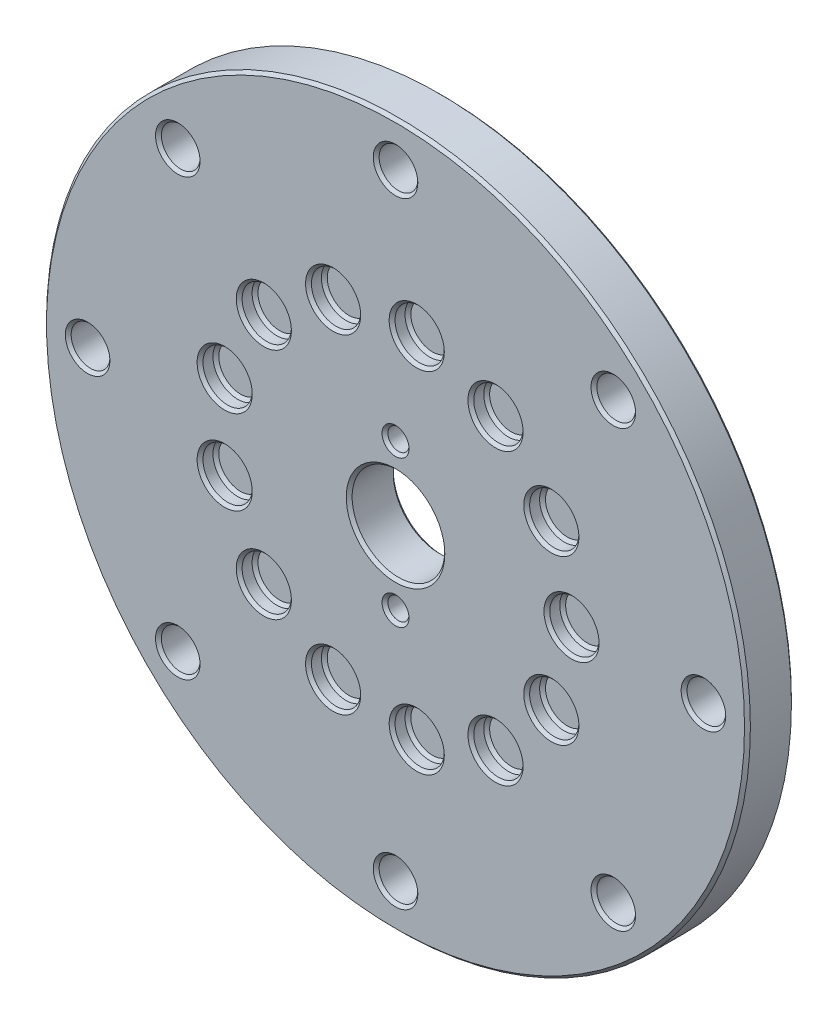
SolidWorks part; units mm, degrees
material "Polylactic Acid (PLA)"
ref_plane "Front Plane" through (0, 0, 0) normal (0, 0, 1) x (1, 0, 0)
ref_plane "Top Plane" through (0, 0, 0) normal (0, 1, 0) x (1, 0, 0)
ref_plane "Right Plane" through (0, 0, 0) normal (1, 0, 0) x (0, 0, -1)
sketch "Sketch1" plane through (0, 0, 0) normal (0, 0, 1) x (1, 0, 0)
  circle A0 centre (0, 0) radius 60
  circle A1 centre (0, 0) radius 7.9
  dimension "D1" = 120
  dimension "D2" = 15.8
extrude "Boss-Extrude1" add sketch "Sketch1" along normal blind 8
sketch "Sketch2" plane through (0, 0, 8) normal (0, 0, 1) x (1, 0, 0)
  circle A0 centre (0, 12.5) radius 1.7 construction
  circle A1 centre (0, 0) radius 12.5 construction
  circle A2 centre (0, -12.5) radius 1.7 construction
  point P0 (0, 12.5)
  point P8 (0, -12.5)
  point P10 (0, 0)
  dimension "D1" = 3.4
  dimension "D2" = 25
  dimension "D3" = 2
sketch "Sketch6" plane through (0, 0, 8) normal (0, 0, 1) x (1, 0, 0)
  circle A0 centre (0, 0) radius 52.5
  circle A1 centre (0, 0) radius 60 construction
  point P6 (0, 52.5)
  point P15 (37.1231, 37.1231)
  point P16 (52.5, 0)
  point P17 (37.1231, -37.1231)
  point P18 (0, -52.5)
  point P19 (-37.1231, -37.1231)
  point P20 (-52.5, 0)
  point P21 (-37.1231, 37.1231)
  dimension "D1" = 7.5
  dimension "D2" = 8
hole_wizard "M6 Clearance Hole1" positions "Sketch6" profile "Sketch5" hole size "M6" standard "ISO" end condition through all
sketch "Sketch5" plane through (-37.1231, 37.1231, 8) normal (1, 0, 0) x (0, -1, 0)
  line L0 (0, 0) -> (0, 8)
  line L1 (0, 8) -> (3.3, 8)
  line L2 (3.3, 8) -> (3.3, 0)
  line L5 (3.3, 0) -> (0, 0)
  line L11 (0, -6.35) -> (0, 107.95) construction
  dimension "Thru Hole Dia." = 6.6
  dimension "Thru Hole Depth" = 8
hole_wizard "M3 Clearance Hole1" positions "Sketch2" profile "Sketch7" hole size "M3" standard "ISO" end condition through all
sketch "Sketch7" plane through (0, 12.5, 8) normal (1, 0, 0) x (0, -1, 0)
  line L0 (0, 0) -> (0, 8)
  line L1 (0, 8) -> (1.8, 8)
  line L2 (1.8, 8) -> (1.8, 0)
  line L5 (1.8, 0) -> (0, 0)
  line L11 (0, -6.35) -> (0, 107.95) construction
  dimension "Thru Hole Dia." = 3.6
  dimension "Thru Hole Depth" = 8
sketch "Sketch8" plane through (0, 0, 8) normal (0, 0, 1) x (1, 0, 0)
  line L0 (-30, 0) -> (30, 0) construction
  line L1 (0, 0) -> (30, 0) construction
  line L2 (0, 0) -> (26.5637, -13.9417) construction
  circle A0 centre (0, 0) radius 30 construction
  circle A1 centre (30, 0) radius 4.2
  circle A2 centre (26.5637, -13.9417) radius 4.2
  circle A3 centre (17.0419, -24.6895) radius 4.2
  circle A4 centre (3.6161, -29.7813) radius 4.2
  circle A5 centre (-10.6381, -28.0505) radius 4.2
  circle A6 centre (-22.4553, -19.8937) radius 4.2
  circle A7 centre (-29.1283, -7.1795) radius 4.2
  circle A8 centre (-29.1283, 7.1795) radius 4.2
  circle A9 centre (-22.4553, 19.8937) radius 4.2
  circle A10 centre (-10.6381, 28.0505) radius 4.2
  circle A11 centre (3.6161, 29.7813) radius 4.2
  circle A12 centre (17.0419, 24.6895) radius 4.2
  circle A13 centre (26.5637, 13.9417) radius 4.2
  dimension "D1" = 60
  dimension "D2" = 8.4
  dimension "D4" = 27.692
  dimension "D3" = 13
extrude "Cut-Extrude1" cut sketch "Sketch8" against normal blind 2.7
chamfer "Chamfer1" distance 0.5 angle 45 50 edges at (-18.2553, -19.8937, 8) (-18.2553, -19.8937, 5.3) (-24.9283, -7.1795, 8) (-24.9283, -7.1795, 5.3) (-24.9283, 7.1795, 8) (-24.9283, 7.1795, 5.3) (-18.2553, 19.8937, 8) (-18.2553, 19.8937, 5.3) (-6.4381, 28.0505, 8) (-6.4381, 28.0505, 5.3) (7.8161, 29.7813, 8) (7.8161, 29.7813, 5.3) (21.2419, 24.6895, 8) (21.2419, 24.6895, 5.3) (7.9, 0, 0) (7.9, 0, 8) (1.8, 12.5, 8) (1.8, 12.5, 0) (1.8, -12.5, 8) (1.8, -12.5, 0) (34.2, 0, 8) (34.2, 0, 5.3) (30.7637, 13.9417, 8) (30.7637, 13.9417, 5.3) (-6.4381, -28.0505, 8) (-6.4381, -28.0505, 5.3) (7.8161, -29.7813, 8) (7.8161, -29.7813, 5.3) (21.2419, -24.6895, 8) (21.2419, -24.6895, 5.3) (30.7637, -13.9417, 8) (30.7637, -13.9417, 5.3) (55.8, 0, 8) (55.8, 0, 0) (40.4231, 37.1231, 8) (40.4231, 37.1231, 0) (3.3, 52.5, 8) (3.3, 52.5, 0) (-33.8231, 37.1231, 8) (-33.8231, 37.1231, 0) (-49.2, 0, 8) (-49.2, 0, 0) (-33.8231, -37.1231, 8) (-33.8231, -37.1231, 0) (3.3, -52.5, 8) (3.3, -52.5, 0) (40.4231, -37.1231, 8) (40.4231, -37.1231, 0) (60, 0, 0) (60, 0, 8)
